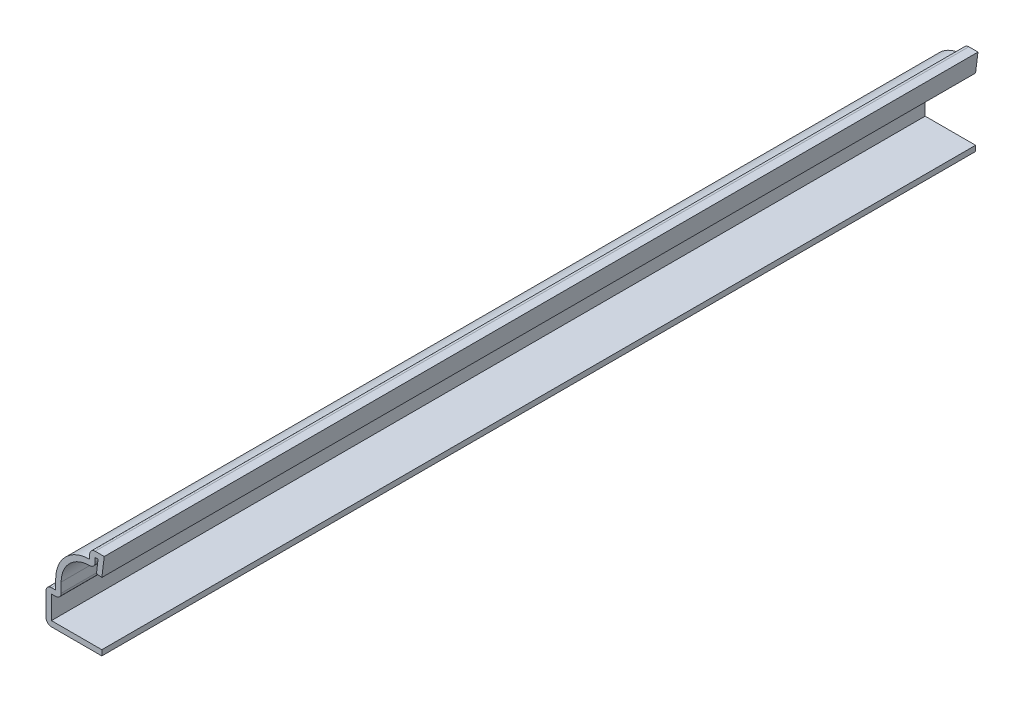
SolidWorks part; units mm, degrees
ref_plane "Front Plane" through (0, 0, 0) normal (0, 0, 1) x (1, 0, 0)
ref_plane "Top Plane" through (0, 0, 0) normal (0, 1, 0) x (1, 0, 0)
ref_plane "Right Plane" through (0, 0, 0) normal (1, 0, 0) x (0, 0, -1)
sketch "Sketch1" plane through (0, 0, 0) normal (0, 0, 1) x (1, 0, 0)
  line L0 (0, 0) -> (-0.3969, 0) construction
  line L1 (-0.3969, 0) -> (-9.525, 0)
  line L2 (-9.525, 0) -> (-9.525, 5.5562)
  line L3 (-9.525, 5.5562) -> (-7.9375, 5.5562)
  line L4 (-7.9375, 5.5562) -> (-7.9375, 7.1437)
  line L5 (-2.3812, 12.7) -> (-2.3813, 14.2875)
  line L6 (-2.3813, 14.2875) -> (0, 14.2875)
  line L7 (0, 14.2875) -> (-0.3969, 11.1125)
  arc A0 (-7.9375, 7.1437) -> (-2.3812, 12.7) centre (-2.3813, 7.1437) cw
  point P9 (0, 0)
  point P13 (0, 0)
  dimension "D5" = 5.5562
  dimension "D1" = 14.2875
  dimension "D2" = 9.525
  dimension "D3" = 2.3813
  dimension "D4" = 3.175
  dimension "D6" = 7.1437
  dimension "D7" = 5.5562
  dimension "D8" = 0.3969
extrude "Extrude-Thin1" add sketch "Sketch1" against normal blind 142.875 thin
fillet "Fillet1" radius 0.889 5 edges at (-9.525, 0, -71.4375) (-9.525, 5.5562, -71.4375) (-7.0485, 4.6672, -71.4375) (-1.4922, 11.7256, -71.4375) (-2.3813, 14.2875, -71.4375)
